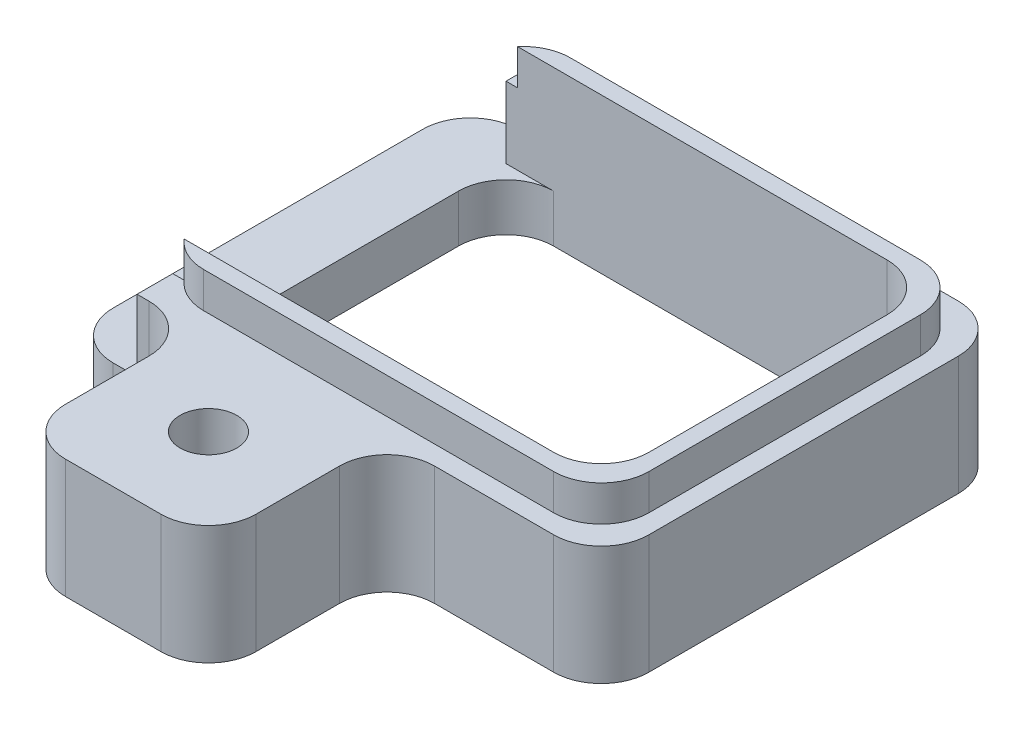
SolidWorks part; units mm, degrees
ref_plane "Front Plane" through (0, 0, 0) normal (0, 0, 1) x (1, 0, 0)
ref_plane "Top Plane" through (0, 0, 0) normal (0, 1, 0) x (1, 0, 0)
ref_plane "Right Plane" through (0, 0, 0) normal (1, 0, 0) x (0, 0, -1)
sketch "Sketch5" plane through (0, 0, 0) normal (0, 1, 0) x (1, 0, 0)
  line L1 (-5.625, -4.25) -> (5.625, -4.25)
  line L2 (-5.625, -4.25) -> (-5.625, 4.25)
  line L3 (-5.625, 4.25) -> (5.625, 4.25)
  line L4 (5.625, -4.25) -> (5.625, 4.25)
  line L5 (-5.625, -4.25) -> (5.625, 4.25) construction
  line L6 (-5.625, 4.25) -> (5.625, -4.25) construction
  point P0 (0, 0)
  dimension "D1" = 8.5
  dimension "D2" = 11.25
extrude "Extrude4" add sketch "Sketch5" along normal blind 2.5
sketch "Sketch19" plane through (0, 2.5, 0) normal (0, 1, 0) x (-1, 0, 0)
  line L0 (5.625, 4.25) -> (-5.625, 4.25) construction
  line L1 (5.625, -4.25) -> (4.125, -4.25)
  line L2 (5.625, -4.25) -> (5.625, 4.25)
  line L3 (5.625, 4.25) -> (4.125, 4.25)
  line L4 (4.125, -4.25) -> (4.125, 4.25)
  dimension "D1" = 1.5
extrude "Extrude12" cut sketch "Sketch19" against normal blind 1.5
sketch "Sketch21" plane through (0, 2.5, 0) normal (0, 1, 0) x (-1, 0, 0)
  line L0 (4.125, 4.25) -> (4.125, -4.25) construction
  line L1 (-4.875, -3.5) -> (4.125, -3.5)
  line L2 (-4.875, -3.5) -> (-4.875, 3.5)
  line L3 (-4.875, 3.5) -> (4.125, 3.5)
  line L4 (4.125, -3.5) -> (4.125, 3.5)
  line L5 (-5.625, -4.25) -> (4.125, -4.25) construction
  line L6 (-5.625, 4.25) -> (-5.625, -4.25) construction
  line L7 (4.125, 4.25) -> (-5.625, 4.25) construction
  dimension "D1" = 0.75
  dimension "D2" = 0.75
  dimension "D3" = 0.75
extrude "Extrude13" cut sketch "Sketch21" against normal through all
sketch "Sketch22" plane through (0, 0, 4.25) normal (0, 0, 1) x (1, 0, 0)
  line L0 (-4.125, 2.5) -> (5.625, 2.5) construction
  line L1 (-2.875, 2.5) -> (1.125, 2.5)
  line L2 (-2.875, 2.5) -> (-2.875, 0)
  line L3 (-2.875, 0) -> (1.125, 0)
  line L4 (1.125, 2.5) -> (1.125, 0)
  line L5 (5.625, 2.5) -> (5.625, 0) construction
  line L6 (-5.625, 0) -> (5.625, 0) construction
  dimension "D1" = 4
  dimension "D2" = 4.5
  dimension "D3" = 0
extrude "Extrude14" add sketch "Sketch22" along normal blind 3.75
sketch "Sketch24" plane through (0, 2.5, 0) normal (0, 1, 0) x (1, 0, 0)
  line L0 (-4.125, 3.85) -> (-4.125, 3.5)
  line L1 (-4.125, 3.5) -> (4.875, 3.5)
  line L2 (4.875, 3.5) -> (4.875, -3.5)
  line L3 (4.875, -3.5) -> (-4.125, -3.5)
  line L4 (-4.125, -3.5) -> (-4.125, -3.85)
  line L9 (-4.125, -3.85) -> (5.225, -3.85)
  line L10 (5.225, -3.85) -> (5.225, 3.85)
  line L11 (5.225, 3.85) -> (-4.125, 3.85)
  line L12 (-4.125, -3.85) -> (5.225, -3.85)
  line L13 (5.225, -3.85) -> (5.225, 3.85)
  line L14 (5.225, 3.85) -> (-4.125, 3.85)
  dimension "D1" = 0.35
extrude "Extrude15" add sketch "Sketch24" along normal blind 0.75
hole_wizard "#0-80 Tapped Hole1" positions "3DSketch1" profile "Sketch26" tap size "#0-80" standard "Ansi Inch"
sketch3d "3DSketch1"
  line L2 (1.125, 2.5, 8) -> (-2.875, 2.5, 8) construction
  line L3 (1.125, 2.5, 8) -> (1.125, 2.5, 4.25) construction
  point P0 (-0.875, 2.5, 6)
  dimension "D1" = 2
  dimension "D2" = 2
sketch "Sketch26" plane through (-0.875, 2.5, 6) normal (1, 0, 0) x (0, 0, 1)
  line L0 (0, 0) -> (0, 79.3679)
  line L1 (0, 79.3679) -> (0.5956, 79.01)
  line L2 (0.5956, 79.01) -> (0.5956, 0)
  line L5 (0.5956, 0) -> (0, 0)
  line L10 (0, 79.3679) -> (-0.5956, 79.01) construction
  line L11 (0, -6.35) -> (0, 107.95) construction
  dimension "Tap Drill Dia." = 1.1913
  dimension "Tap Drill Depth" = 79.01
  dimension "Drill Angle" = 118
fillet "Fillet4" radius 1 14 edges at (5.625, 1.25, -4.25) (5.225, 2.875, -3.85) (5.625, 1.25, 4.25) (5.225, 2.875, 3.85) (4.875, 1.625, 3.5) (4.875, 1.625, -3.5) (-4.125, 0.5, 3.5) (-4.125, 0.5, -3.5) (-5.625, 0.5, -4.25) (-5.625, 0.5, 4.25) (-2.875, 1.25, 8) (1.125, 1.25, 8)
sketch "Sketch28" plane through (0, 3.25, 0) normal (0, 1, 0) x (-1, 0, 0)
  line L0 (3.125, -3.85) -> (4.125, -3.85)
  line L1 (4.125, -3.85) -> (4.125, -2.85)
  arc A1 (4.125, -2.85) -> (3.125, -3.85) centre (3.125, -2.85) cw
extrude "Extrude16" cut sketch "Sketch28" against normal up to surface (0.75 mm away) up to face at (-0.875, 2.5, 6.5956)
sketch "Sketch31" plane through (0, 3.25, 0) normal (0, 1, 0) x (-1, 0, 0)
  line L0 (4.125, 2.85) -> (4.125, 3.85)
  line L1 (4.125, 3.85) -> (3.125, 3.85)
  arc A1 (4.125, 2.85) -> (3.125, 3.85) centre (3.125, 2.85) ccw
extrude "Extrude17" cut sketch "Sketch31" against normal up to surface (0.75 mm away) up to face at (-0.875, 2.5, 6.5956)
